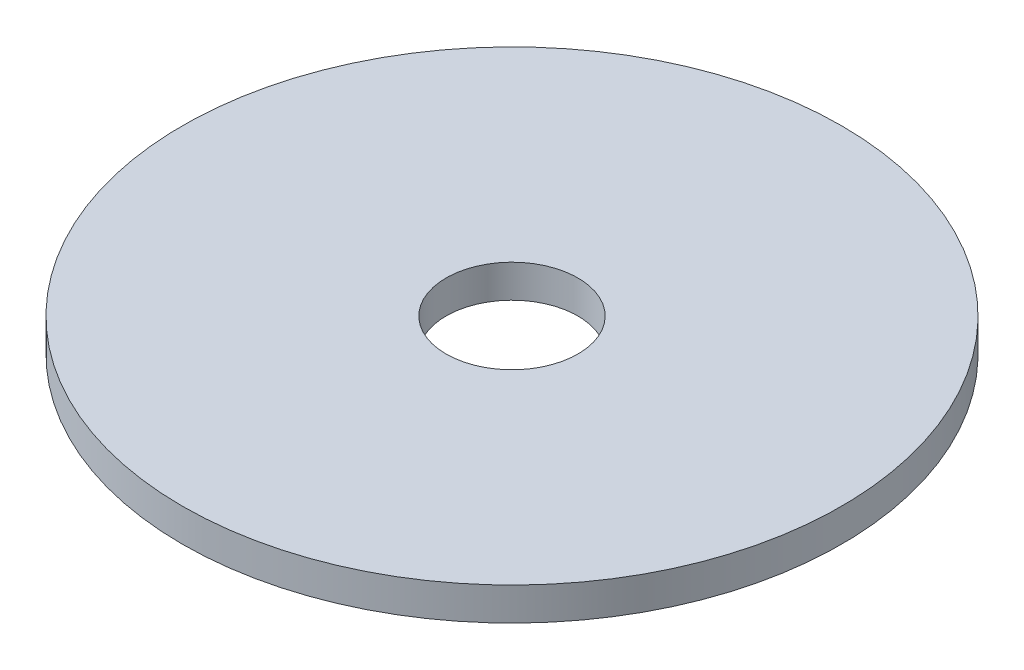
SolidWorks part; units mm, degrees
material "AISI 1020"
ref_plane "Front Plane" through (0, 0, 0) normal (0, 0, 1) x (1, 0, 0)
ref_plane "Top Plane" through (0, 0, 0) normal (0, 1, 0) x (1, 0, 0)
ref_plane "Right Plane" through (0, 0, 0) normal (1, 0, 0) x (0, 0, -1)
sketch "Sketch1" plane through (0, 0, 0) normal (0, 1, 0) x (1, 0, 0)
  circle A0 centre (0, 0) radius 63.5
  circle A1 centre (0, 0) radius 12.7
  dimension "D1" = 127
  dimension "D2" = 25.4
extrude "Boss-Extrude1" add sketch "Sketch1" along normal blind 6.35
